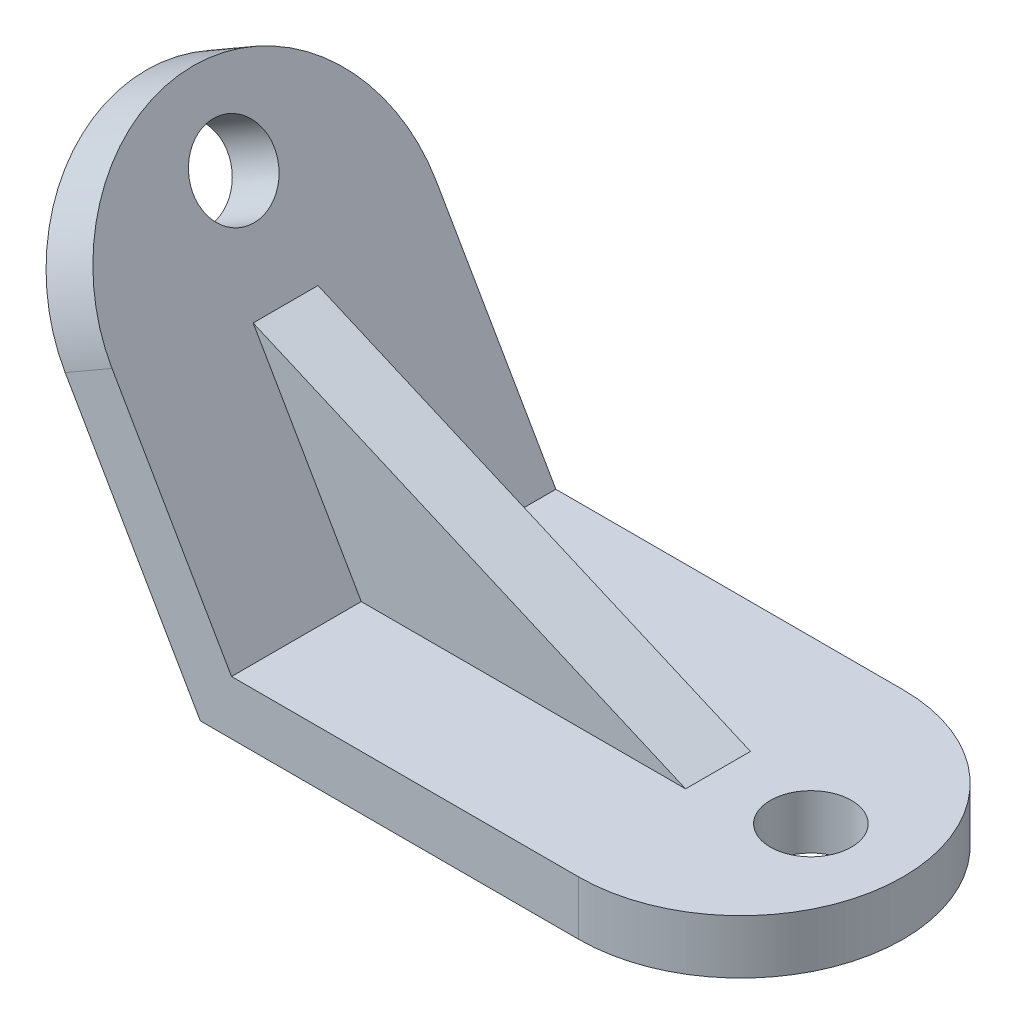
SolidWorks part; units mm, degrees
ref_plane "Front Plane" through (0, 0, 0) normal (0, 0, 1) x (1, 0, 0)
ref_plane "Top Plane" through (0, 0, 0) normal (0, 1, 0) x (1, 0, 0)
ref_plane "Right Plane" through (0, 0, 0) normal (1, 0, 0) x (0, 0, -1)
sketch "Sketch2" plane through (0, 0, 0) normal (0, 0, 1) x (1, 0, 0)
  line L0 (100, 0) -> (0, 0)
  line L1 (0, 0) -> (-40, 69.282)
  line L2 (100, 10) -> (5.7735, 10)
  line L3 (5.7735, 10) -> (-31.3397, 74.282)
  line L4 (-40, 69.282) -> (-31.3397, 74.282)
  line L5 (100, 0) -> (100, 10)
  dimension "D1" = 100
  dimension "D2" = 80
  dimension "D3" = 120
  dimension "D4" = 10
extrude "Boss-Extrude1" add sketch "Sketch2" along normal mid plane 60
sketch "Sketch3" plane through (0, 10, 0) normal (0, 1, 0) x (1, 0, 0)
  line L0 (100, -30) -> (100, 30) construction
  line L1 (100, -30) -> (5.7735, -30) construction
  line L2 (100, 30) -> (5.7735, 30) construction
  line L3 (100, -30) -> (70, -30)
  line L4 (100, -30) -> (100, 30)
  line L5 (100, 30) -> (70, 30)
  arc A0 (70, -30) -> (70, 30) centre (70, 0) ccw
  line M1 (100, 30) -> (5.7735, 30)
  line M3 (5.7735, -30) -> (100, -30)
  line M4 (100, -30) -> (100, 30)
  dimension "D1" = 30
extrude "Cut-Extrude1" cut sketch "Sketch3" against normal blind 60 contours A0 L4 M1 | A0 M3 M4
sketch "Sketch4" plane through (8.6603, 5, 0) normal (0.866, 0.5, 0) x (0, 0, -1)
  line L0 (-30, 80) -> (30, 80) construction
  line L1 (30, 5.7735) -> (30, 80) construction
  line L2 (-30, 5.7735) -> (-30, 80) construction
  line L3 (30, 50) -> (30, 80)
  line L4 (-30, 50) -> (-30, 80)
  line L5 (-30, 80) -> (30, 80)
  arc A0 (30, 50) -> (-30, 50) centre (0, 50) ccw
  point P4 (0, 80)
  line M1 (30, 5.7735) -> (30, 80)
  line M2 (30, 80) -> (-30, 80)
  line M3 (-30, 80) -> (-30, 5.7735)
  dimension "D1" = 30
extrude "Cut-Extrude2" cut sketch "Sketch4" against normal blind 60 contours A0 L5 M3 | A0 M1 M2
sketch "Sketch5" plane through (0, 0, 0) normal (0, 0, 1) x (1, 0, 0)
  line L0 (5.7735, 10) -> (65.7735, 10)
  line L1 (70, 10) -> (5.7735, 10) construction
  line L2 (5.7735, 10) -> (-14.2265, 44.641)
  line L3 (5.7735, 10) -> (-16.3397, 48.3013) construction
  line L4 (-14.2265, 44.641) -> (65.7735, 10)
  dimension "D1" = 40
  dimension "D2" = 60
extrude "Boss-Extrude2" add sketch "Sketch5" along normal mid plane 12
sketch "Sketch6" plane through (0, 10, 0) normal (0, 1, 0) x (1, 0, 0)
  circle A0 centre (82.9515, 0) radius 7.5
  dimension "D1" = 15
extrude "Cut-Extrude3" cut sketch "Sketch6" against normal blind 12
sketch "Sketch7" plane through (0, 0, 0) normal (-0.866, -0.5, 0) x (0, 0, 1)
  circle A0 centre (0, 64.9526) radius 7.5
  dimension "D1" = 15
extrude "Cut-Extrude4" cut sketch "Sketch7" against normal blind 12
